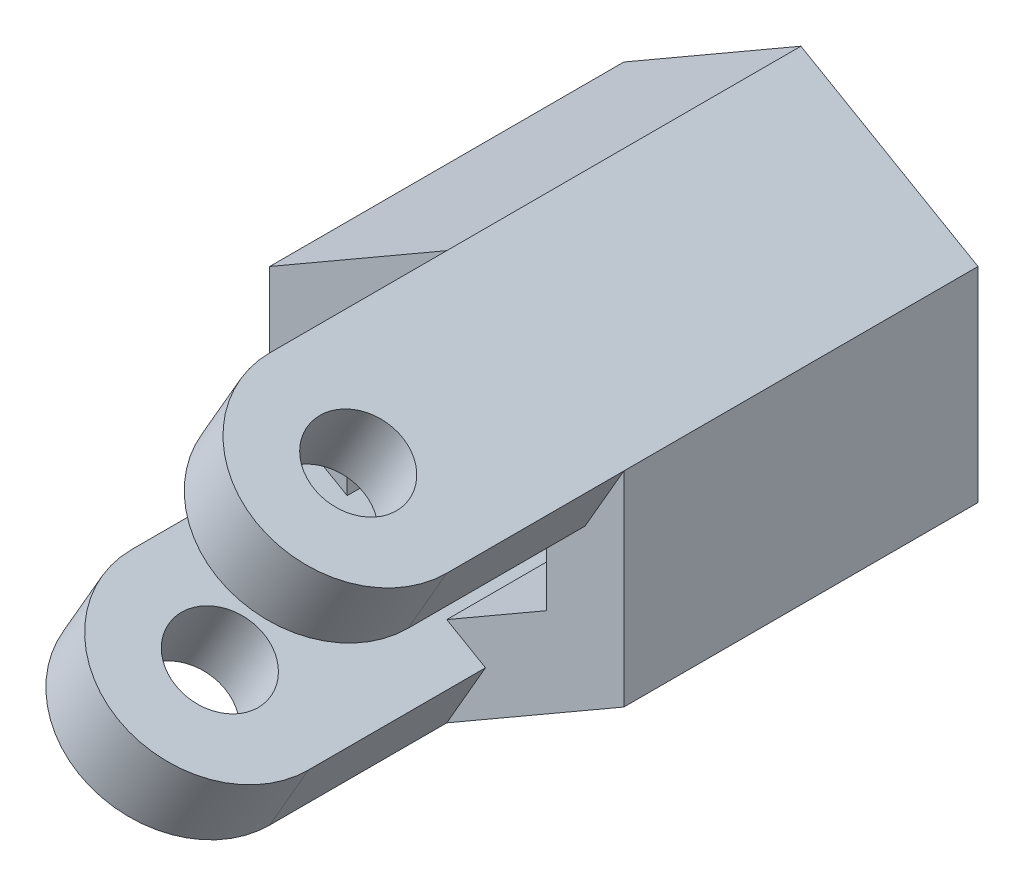
SolidWorks part; units mm, degrees
ref_plane "정면" through (0, 0, 0) normal (0, 0, 1) x (1, 0, 0)
ref_plane "윗면" through (0, 0, 0) normal (0, 1, 0) x (1, 0, 0)
ref_plane "우측면" through (0, 0, 0) normal (1, 0, 0) x (0, 0, -1)
sketch "스케치1" plane through (0, 0, 0) normal (0, 0, 1) x (1, 0, 0)
  line L1 (0, 2.5981) -> (-2.25, 1.299)
  line L2 (-2.25, 1.299) -> (-2.25, -1.299)
  line L3 (-2.25, -1.299) -> (0, -2.5981)
  line L4 (0, -2.5981) -> (2.25, -1.299)
  line L5 (2.25, -1.299) -> (2.25, 1.299)
  line L6 (2.25, 1.299) -> (0, 2.5981)
  line L7 (0, 4.6188) -> (-4, 2.3094)
  line L8 (-4, 2.3094) -> (-4, -2.3094)
  line L9 (-4, -2.3094) -> (0, -4.6188)
  line L10 (0, -4.6188) -> (4, -2.3094)
  line L11 (4, -2.3094) -> (4, 2.3094)
  line L12 (4, 2.3094) -> (0, 4.6188)
  circle A0 centre (0, 0) radius 2.25 construction
  circle A1 centre (0, 0) radius 4 construction
  point P1 (0, 0)
  dimension "D1" = 4.5
  dimension "D2" = 8
extrude "보스-돌출1" add sketch "스케치1" along normal blind 6
sketch "스케치2" plane through (0, 0, 0) normal (0, 0, -1) x (-1, 0, 0)
  line L1 (0, 4.6188) -> (-4, 2.3094)
  line L2 (-4, 2.3094) -> (-4, -2.3094)
  line L3 (-4, -2.3094) -> (0, -4.6188)
  line L4 (0, -4.6188) -> (4, -2.3094)
  line L5 (4, -2.3094) -> (4, 2.3094)
  line L6 (4, 2.3094) -> (0, 4.6188)
  circle A0 centre (0, 0) radius 4 construction
  circle A1 centre (0, 0) radius 1.25
  dimension "D1" = 2.5
extrude "보스-돌출2" add sketch "스케치2" along normal blind 2
sketch "스케치3" plane through (2, 3.4641, 0) normal (0.5, 0.866, 0) x (0.866, -0.5, 0)
  line L0 (2.3094, -6) -> (2.3094, 2) construction
  line L1 (-2.3094, -6) -> (2.3094, -6)
  line L2 (-2.3094, -6) -> (-2.3094, -10)
  line L4 (2.3094, -6) -> (2.3094, -10)
  arc A0 (-2.3094, -10) -> (2.3094, -10) centre (0, -10) ccw
  circle A1 centre (0, -10) radius 1
  dimension "D2" = 2
  dimension "D1" = 4
extrude "보스-돌출4" add sketch "스케치3" against normal up to surface (1.75 mm away) up to face at (1.125, 1.9486, 3)
sketch "스케치4" plane through (-2, -3.4641, 0) normal (-0.5, -0.866, 0) x (0.866, -0.5, 0)
  line L2 (-2.3094, 10) -> (-2.3094, 6)
  line L3 (-2.3094, 6) -> (2.3094, 6)
  line L4 (2.3094, 10) -> (2.3094, 6)
  arc A0 (2.3094, 10) -> (-2.3094, 10) centre (0, 10) ccw
  arc A1 (2.3094, 10) -> (-2.3094, 10) centre (0, 10) ccw construction
  circle A2 centre (0, 10) radius 1
  point P1 (2.3094, 6)
  point P13 (2.3094, 10)
  dimension "D1" = 2
extrude "보스-돌출7" add sketch "스케치4" against normal up to surface (1.75 mm away) up to face at (-1.125, -1.9486, 3)
